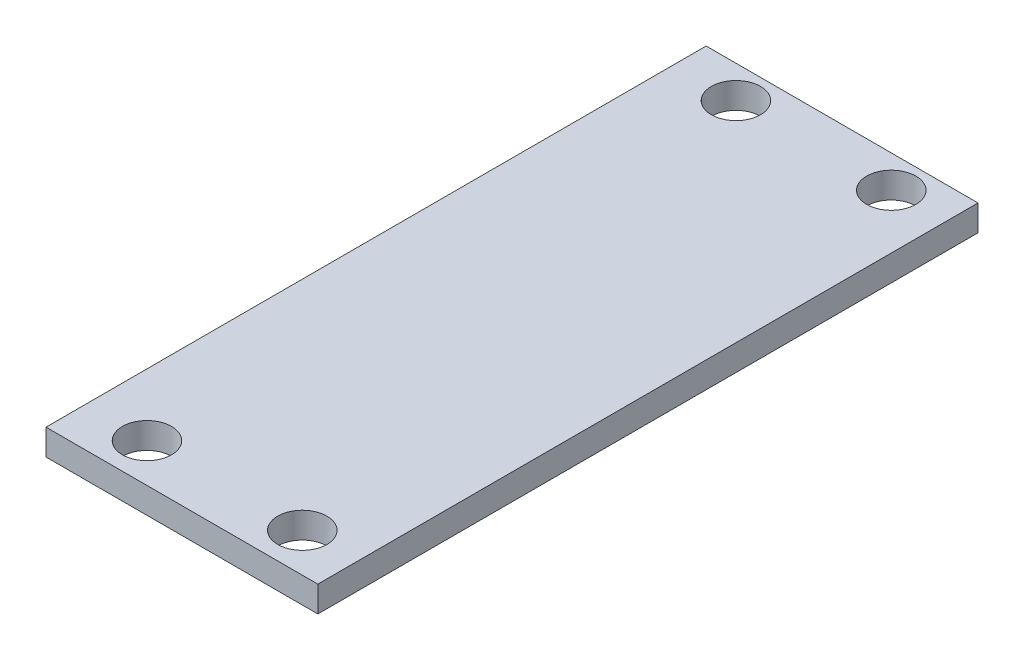
SolidWorks part; units mm, degrees
ref_plane "Front Plane" through (0, 0, 0) normal (0, 0, 1) x (1, 0, 0)
ref_plane "Top Plane" through (0, 0, 0) normal (0, 1, 0) x (1, 0, 0)
ref_plane "Right Plane" through (0, 0, 0) normal (1, 0, 0) x (0, 0, -1)
sketch "Sketch1" plane through (0, 0, 0) normal (0, 1, 0) x (1, 0, 0)
  line L1 (-14.445, 13.0187) -> (6.555, 13.0187)
  line L2 (-14.445, 13.0187) -> (-14.445, -37.9813)
  line L3 (-14.445, -37.9813) -> (6.555, -37.9813)
  line L4 (6.555, 13.0187) -> (6.555, -37.9813)
  circle A0 centre (-9.645, 10.5187) radius 1.9
  circle A1 centre (2.355, 10.5187) radius 1.9
  circle A2 centre (2.355, -34.9813) radius 1.9
  circle A3 centre (-9.645, -34.9813) radius 1.9
  dimension "D3" = 3.8
  dimension "D1" = 21
  dimension "D2" = 51
  dimension "D4" = 4.8
  dimension "D5" = 2.5
  dimension "D6" = 2
  dimension "D7" = 2
extrude "Boss-Extrude1" add sketch "Sketch1" along normal blind 2
